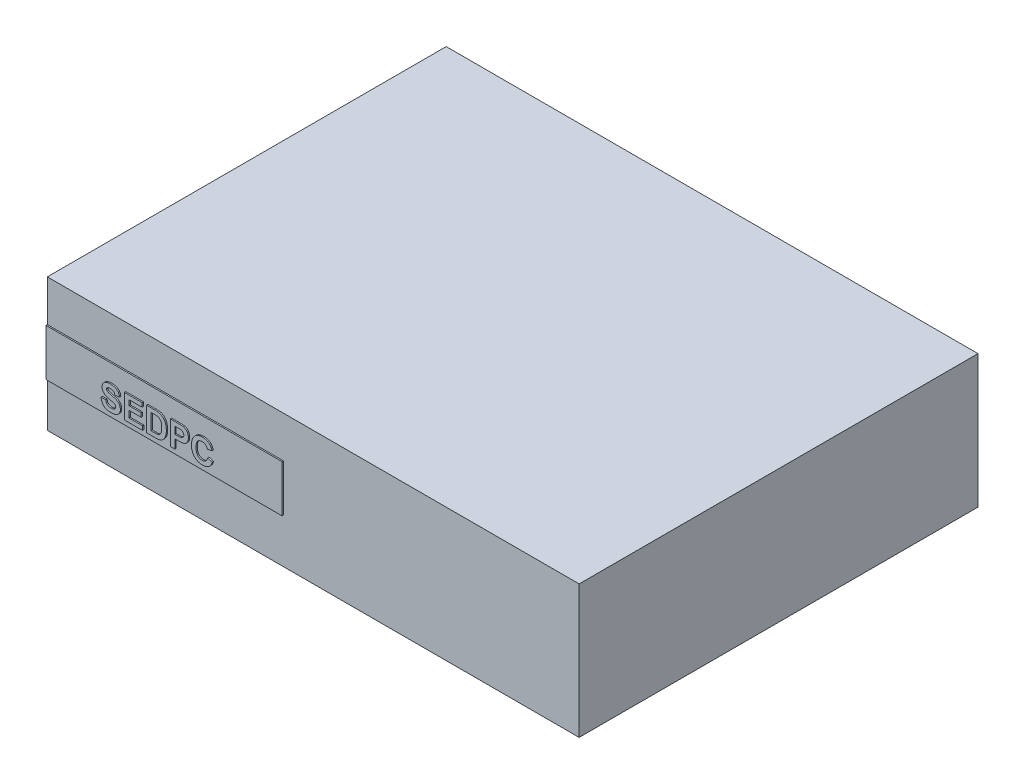
SolidWorks part; units mm, degrees
ref_plane "Alzado" through (0, 0, 0) normal (0, 0, 1) x (1, 0, 0)
ref_plane "Planta" through (0, 0, 0) normal (0, 1, 0) x (1, 0, 0)
ref_plane "Vista lateral" through (0, 0, 0) normal (1, 0, 0) x (0, 0, -1)
sketch "Croquis1" plane through (0, 0, 0) normal (0, 0, 1) x (1, 0, 0)
  line L1 (0, 0) -> (400, 0)
  line L2 (0, 0) -> (0, -100)
  line L3 (0, -100) -> (400, -100)
  line L4 (400, 0) -> (400, -100)
  dimension "D1" = 100
  dimension "D2" = 400
extrude "Saliente-Extruir1" add sketch "Croquis1" along normal blind 300
sketch "Croquis2" plane through (0, 0, 300) normal (0, 0, 1) x (1, 0, 0)
  line L0 (0, 0) -> (0, -100) construction
  line L1 (0, -31.1121) -> (177.5835, -31.1121)
  line L2 (0, -31.1121) -> (0, -66.3972)
  line L3 (0, -66.3972) -> (177.5835, -66.3972)
  line L4 (177.5835, -31.1121) -> (177.5835, -66.3972)
extrude "Saliente-Extruir2" add sketch "Croquis2" along normal blind 1
sketch "Croquis3" plane through (0, 0, 301) normal (0, 0, 1) x (1, 0, 0)
  line L0 (0, -62.246) -> (171.7719, -62.246) construction
  line L1 (0, -31.1121) -> (0, -66.3972) construction
  text T0 "      SEDPC" font "Arial" height in points 70
extrude "Saliente-Extruir3" add sketch "Croquis3" along normal blind 1
